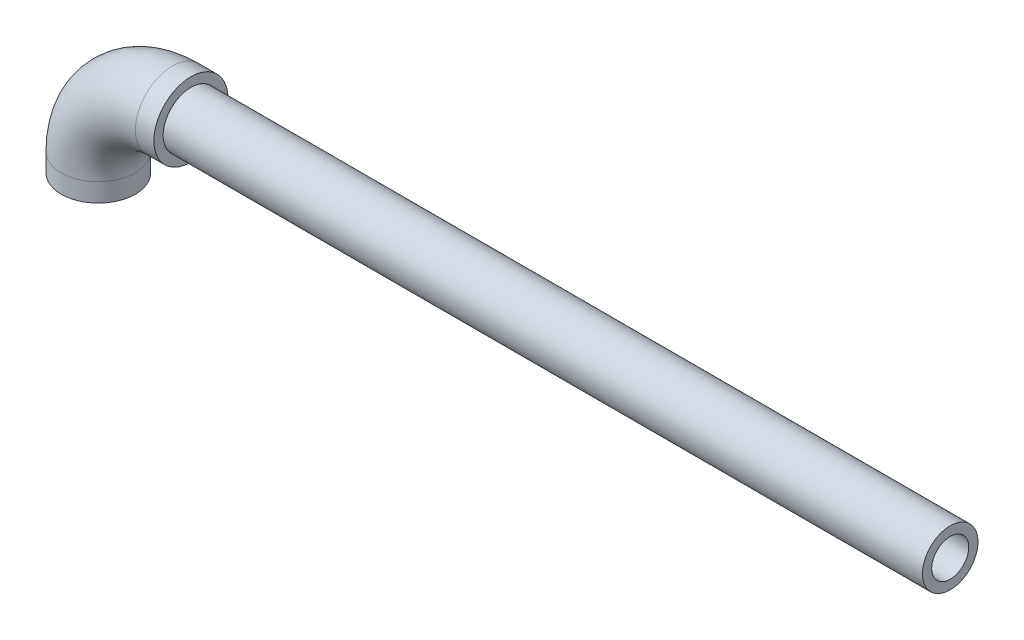
SolidWorks part; units mm, degrees
ref_plane "Front Plane" through (0, 0, 0) normal (0, 0, 1) x (1, 0, 0)
ref_plane "Top Plane" through (0, 0, 0) normal (0, 1, 0) x (1, 0, 0)
ref_plane "Right Plane" through (0, 0, 0) normal (1, 0, 0) x (0, 0, -1)
sketch "Sketch1" plane through (0, 0, 0) normal (0, 1, 0) x (1, 0, 0)
  circle A0 centre (0, 0) radius 20
  circle A1 centre (0, 0) radius 15
  dimension "D1" = 40
  dimension "D2" = 30
sketch "Sketch2" plane through (0, 0, 0) normal (0, 0, 1) x (1, 0, 0)
  line L0 (0, 0) -> (0, 10)
  line L1 (40, 50) -> (50, 50)
  arc A0 (0, 10) -> (40, 50) centre (40, 10) cw
  dimension "D1" = 40
  dimension "D2" = 10
  dimension "D3" = 10
sweep "Sweep1" add profiles "Sketch1" path "Sketch2"
sketch "Sketch3" plane through (50, 0, 0) normal (1, 0, 0) x (0, 0, -1)
  circle A0 centre (0, 50) radius 15
  circle A1 centre (0, 50) radius 10
  dimension "D1" = 5
extrude "Boss-Extrude1" add sketch "Sketch3" along normal blind 410 separate body
